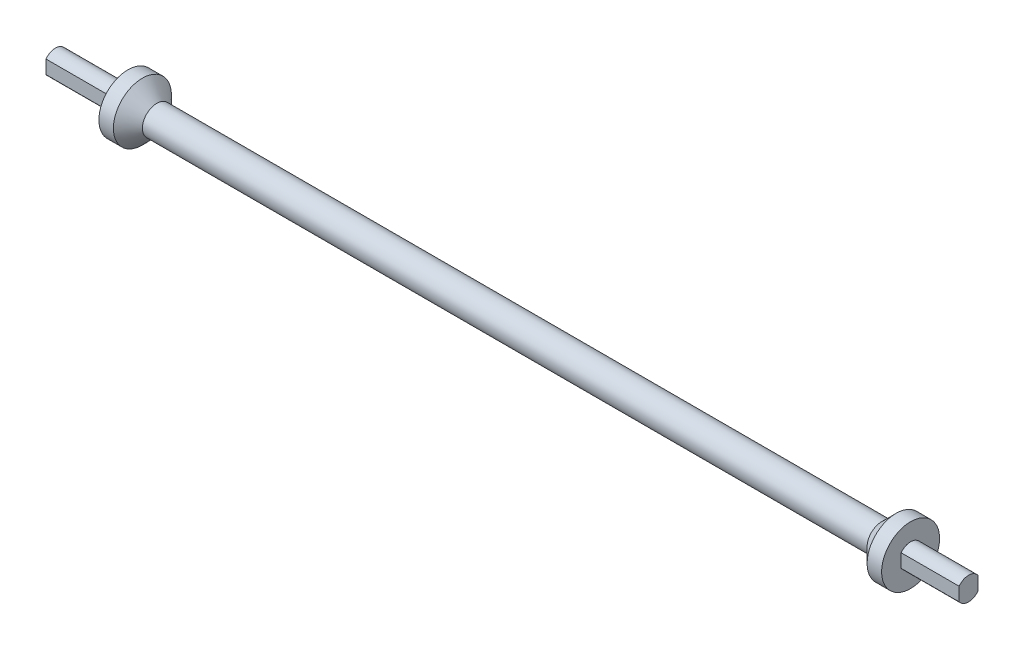
SolidWorks part; units mm, degrees
material "6061 Alloy"
ref_plane "Front Plane" through (0, 0, 0) normal (0, 0, 1) x (1, 0, 0)
ref_plane "Top Plane" through (0, 0, 0) normal (0, 1, 0) x (1, 0, 0)
ref_plane "Right Plane" through (0, 0, 0) normal (1, 0, 0) x (0, 0, -1)
sketch "Sketch1" plane through (0, 0, 0) normal (0, 0, 1) x (1, 0, 0)
  line L0 (0, 68.7671) -> (0, -57.4587) construction
  line L1 (-25.3674, 0) -> (33.9251, 0) construction
  line L2 (-125, 5) -> (125, 5)
  line L3 (125, 5) -> (130, 10)
  line L4 (130, 10) -> (135, 10)
  line L5 (135, 10) -> (135, 4)
  line L6 (135, 4) -> (155, 4)
  line L7 (155, 4) -> (155, -4) construction
  line L8 (-155, 4) -> (-155, -4) construction
  line L9 (-135, 4) -> (-155, 4)
  line L10 (-135, 10) -> (-135, 4)
  line L11 (-130, 10) -> (-135, 10)
  line L12 (-125, 5) -> (-130, 10)
  line L13 (-155, 0) -> (155, 0)
  line L14 (-125, -5) -> (-130, -10) construction
  line L15 (-130, -10) -> (-135, -10) construction
  line L16 (-135, -10) -> (-135, -4) construction
  line L17 (-135, -4) -> (-155, -4) construction
  line L18 (135, -4) -> (155, -4) construction
  line L19 (135, -10) -> (135, -4) construction
  line L20 (130, -10) -> (135, -10) construction
  line L21 (125, -5) -> (130, -10) construction
  line L22 (-125, -5) -> (125, -5) construction
  line L23 (-155, 4) -> (-155, 0)
  line L24 (155, 4) -> (155, 0)
  point P18 (0, 5)
  point P28 (0, -5)
  dimension "D1" = 270
  dimension "D2" = 20
  dimension "D3" = 5
  dimension "D4" = 135
  dimension "D5" = 8
  dimension "D6" = 20
  dimension "D7" = 10
revolve "Revolve3" add sketch "Sketch1" angle 360 about L1
sketch "Sketch3" plane through (-155, 0, 0) normal (-1, 0, 0) x (0, 0, 1)
  circle A0 centre (0, 0) radius 4 construction
  circle A1 centre (0, 0) radius 4
extrude "Boss-Extrude3" add sketch "Sketch3" along normal offset from surface (5 mm away) 25 up to face at (-135, 0, 4) offset beyond the face yes
sketch "Sketch2" plane through (0, 0, 0) normal (0, 1, 0) x (1, 0, 0)
  line L0 (-160, 0) -> (155, 0) construction
  line L3 (-160, 4) -> (-160, -4) construction
  line L4 (155, -4) -> (155, 4) construction
  line L5 (-135, 10) -> (-135, -10) construction
  line L6 (-160, 4) -> (-135, 4)
  line L7 (-160, 4) -> (-160, 3.25)
  line L8 (-160, 3.25) -> (-135, 3.25)
  line L9 (-135, 4) -> (-135, 3.25)
  line L10 (155, -4) -> (155, -3.25)
  line L11 (135, 4) -> (155, 4)
  line L14 (135, 4) -> (135, 3.25)
  line L15 (135, 3.25) -> (155, 3.25)
  line L16 (155, 4) -> (155, 3.25)
  line L17 (135, -3.25) -> (155, -3.25)
  line L18 (135, -4) -> (135, -3.25)
  line L19 (135, -4) -> (155, -4)
  line L20 (-135, -4) -> (-135, -3.25)
  line L21 (-160, -3.25) -> (-135, -3.25)
  line L22 (-160, -4) -> (-160, -3.25)
  line L23 (-160, -4) -> (-135, -4)
  dimension "D1" = 6.5
extrude "Cut-Extrude1" cut sketch "Sketch2" along normal through all and the other way through all
